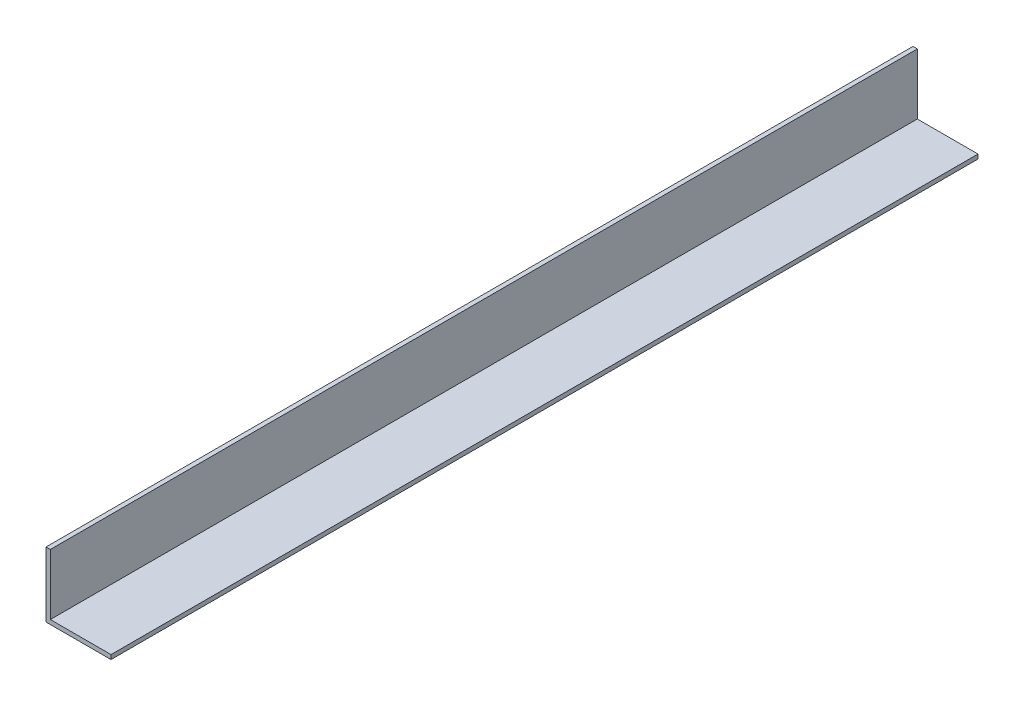
SolidWorks part; units mm, degrees
ref_plane "Спереди" through (0, 0, 0) normal (0, 0, 1) x (1, 0, 0)
ref_plane "Сверху" through (0, 0, 0) normal (0, 1, 0) x (1, 0, 0)
ref_plane "Справа" through (0, 0, 0) normal (1, 0, 0) x (0, 0, -1)
sketch "Эскиз1" plane through (0, 0, 0) normal (0, 0, 1) x (1, 0, 0)
  line L0 (0, 0) -> (15, 0)
  line L1 (15, 0) -> (15, 1)
  line L2 (15, 1) -> (1, 1)
  line L3 (1, 1) -> (1, 15)
  line L4 (1, 15) -> (0, 15)
  line L5 (0, 15) -> (0, 0)
  dimension "D1" = 15
  dimension "D2" = 15
  dimension "D3" = 1
  dimension "D4" = 1
extrude "Бобышка-Вытянуть1" add sketch "Эскиз1" along normal blind 200
